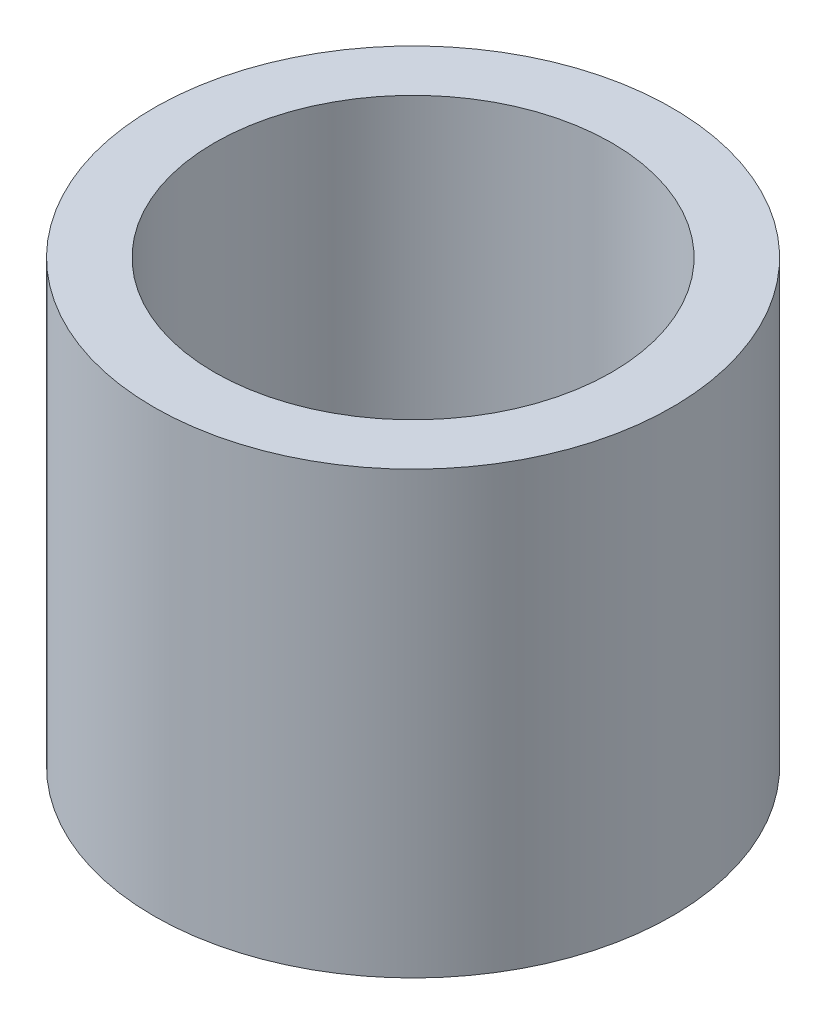
SolidWorks part; units mm, degrees
ref_plane "Front" through (0, 0, 0) normal (0, 0, 1) x (1, 0, 0)
ref_plane "Top" through (0, 0, 0) normal (0, 1, 0) x (1, 0, 0)
ref_plane "Right" through (0, 0, 0) normal (1, 0, 0) x (0, 0, -1)
sketch "Sketch1" plane through (0, 0, 0) normal (0, 1, 0) x (1, 0, 0)
  circle A0 centre (0, 0) radius 4.572
  circle A1 centre (0, 0) radius 3.5052
  dimension "D1" = 9.144
  dimension "D2" = 7.0104
extrude "Extrude1" add sketch "Sketch1" along normal blind 7.7724
